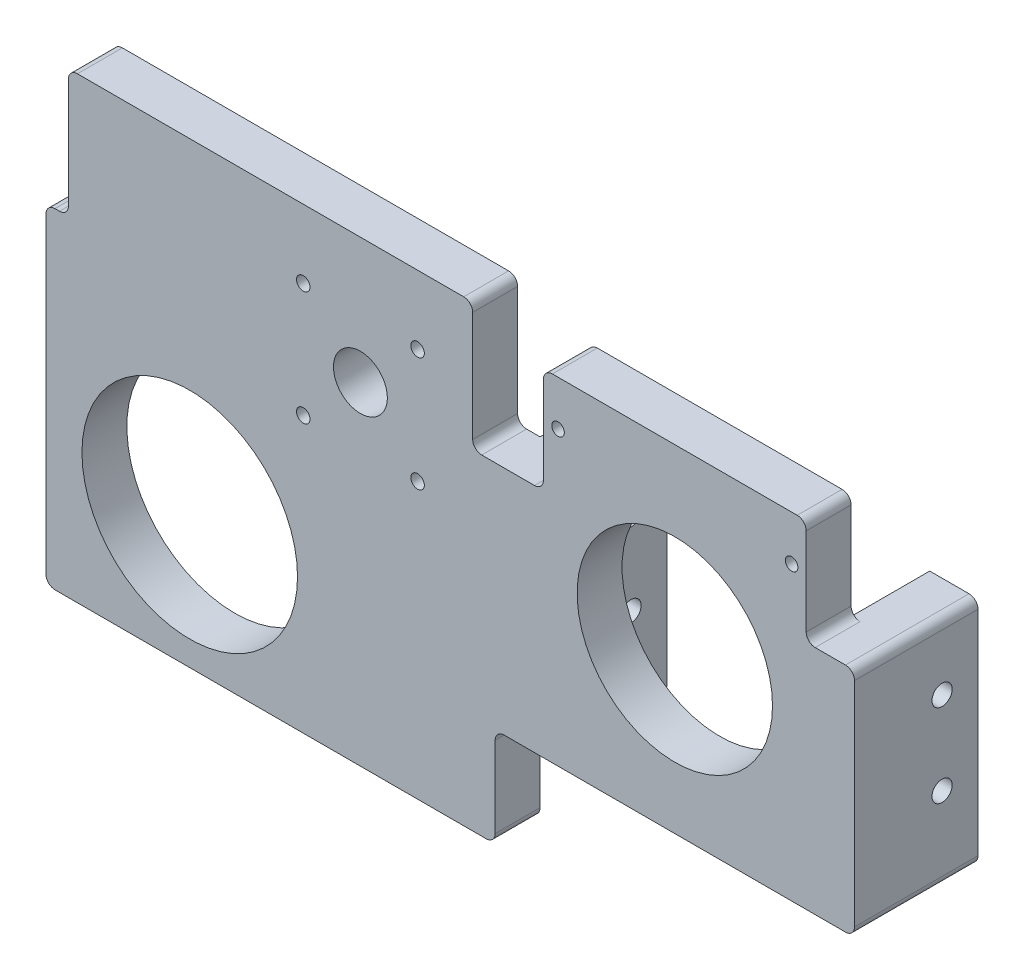
SolidWorks part; units mm, degrees
ref_plane "Front Plane" through (0, 0, 0) normal (0, 0, 1) x (1, 0, 0)
ref_plane "Top Plane" through (0, 0, 0) normal (0, 1, 0) x (1, 0, 0)
ref_plane "Right Plane" through (0, 0, 0) normal (1, 0, 0) x (0, 0, -1)
sketch "Sketch1" plane through (0, 0, 0) normal (0, 1, 0) x (1, 0, 0)
  line L0 (0, 0) -> (0, -3.75) construction
  line L1 (-40, -13.75) -> (40, -13.75)
  line L2 (-40, -13.75) -> (-40, 13.75)
  line L3 (-40, 13.75) -> (-29.25, 13.75)
  line L4 (40, -13.75) -> (40, 13.75)
  line L5 (-40, -13.75) -> (40, 13.75) construction
  line L6 (-40, 13.75) -> (40, -13.75) construction
  line L8 (-29.25, 13.75) -> (-29.25, -3.75)
  line L9 (-29.25, -3.75) -> (29.25, -3.75)
  line L10 (29.25, 13.75) -> (29.25, -3.75)
  line L11 (29.25, 13.75) -> (40, 13.75)
  point P0 (0, 0)
  dimension "D1" = 80
  dimension "D2" = 27.5
  dimension "D3" = 10.75
  dimension "D4" = 10
extrude "Boss-Extrude1" add sketch "Sketch1" along normal blind 80
sketch "Sketch2" plane through (0, 0, 13.75) normal (0, 0, 1) x (1, 0, 0)
  line L0 (0, 0) -> (0, 35.5) construction
  line L1 (-40, 0) -> (40, 0) construction
  circle A0 centre (0, 35.5) radius 21.75
  dimension "D2" = 43.5
  dimension "D1" = 35.5
extrude "Cut-Extrude1" cut sketch "Sketch2" against normal blind 10
sketch "Sketch3" plane through (0, 0, 13.75) normal (0, 0, 1) x (1, 0, 0)
  line L0 (0, 35.5) -> (0, 80) construction
  line L1 (-40, 80) -> (40, 80) construction
  line L2 (0, 65) -> (26, 65) construction
  circle A1 centre (26, 65) radius 1.4
  circle A2 centre (-26, 65) radius 1.4
  dimension "D1" = 26
  dimension "D3" = 2.8
  dimension "D2" = 29.5
extrude "Cut-Extrude2" cut sketch "Sketch3" against normal blind 4
sketch "Sketch4" plane through (0, 0, 3.75) normal (0, 0, -1) x (-1, 0, 0)
  line L0 (0, 35.5) -> (0, 80) construction
  line L1 (-29.25, 80) -> (29.25, 80) construction
  line L2 (-29.25, 65) -> (29.25, 65) construction
  line L3 (29.25, 80) -> (29.25, 0) construction
  line L4 (-27.21, 62.9042) -> (-28.42, 65)
  line L5 (28.42, 65) -> (27.21, 67.0958)
  line L6 (27.21, 67.0958) -> (24.79, 67.0958)
  line L7 (24.79, 67.0958) -> (23.58, 65)
  line L8 (23.58, 65) -> (24.79, 62.9042)
  line L9 (24.79, 62.9042) -> (27.21, 62.9042)
  line L10 (27.21, 62.9042) -> (28.42, 65)
  line L11 (-24.79, 62.9042) -> (-27.21, 62.9042)
  line L12 (-23.58, 65) -> (-24.79, 62.9042)
  line L13 (-24.79, 67.0958) -> (-23.58, 65)
  line L14 (-27.21, 67.0958) -> (-24.79, 67.0958)
  line L15 (-28.42, 65) -> (-27.21, 67.0958)
  circle A0 centre (26, 65) radius 2.0958 construction
  circle A1 centre (-26, 65) radius 2.0958 construction
  point P21 (0, 65)
  dimension "D1" = 29.5
  dimension "D2" = 26
  dimension "D3" = 2.42
extrude "Cut-Extrude3" cut sketch "Sketch4" against normal blind 6
sketch "Sketch5" plane through (40, 0, 0) normal (1, 0, 0) x (0, 0, -1)
  line L0 (5.75, 0) -> (5.75, 80) construction
  line L1 (-13.75, 0) -> (13.75, 0) construction
  line L2 (-13.75, 80) -> (13.75, 80) construction
  line L3 (-13.75, 80) -> (-13.75, 0) construction
  circle A0 centre (5.75, 18.5) radius 2.25
  circle A1 centre (5.75, 37) radius 2.25
  dimension "D3" = 4.5
  dimension "D1" = 18.5
  dimension "D2" = 18.5
  dimension "D4" = 19.5
extrude "Cut-Extrude4" cut sketch "Sketch5" against normal through all
sketch "Sketch6" plane through (0, 0, 13.75) normal (0, 0, 1) x (1, 0, 0)
  line L0 (0, 0) -> (0, 80) construction
  line L1 (-40, 80) -> (-29.25, 80)
  line L2 (-40, 80) -> (-40, 51.5)
  line L3 (-40, 51.5) -> (-29.25, 51.5)
  line L4 (-29.25, 80) -> (-29.25, 51.5)
  line L5 (-40, 0) -> (40, 0) construction
  line L6 (-40, 80) -> (40, 80) construction
  line L7 (40, 51.5) -> (29.25, 51.5)
  line L8 (40, 80) -> (29.25, 80)
  line L9 (29.25, 80) -> (29.25, 51.5)
  line L10 (40, 80) -> (40, 51.5)
  dimension "D1" = 10.75
  dimension "D2" = 28.5
extrude "Cut-Extrude5" cut sketch "Sketch6" against normal through all
sketch "Sketch7" plane through (-40, 0, 0) normal (-1, 0, 0) x (0, 0, 1)
  line L0 (3.75, 0) -> (3.75, -22)
  line L2 (13.75, 0) -> (13.75, 80)
  line L3 (13.75, 80) -> (3.75, 80)
  line L4 (3.75, 0) -> (3.75, 80)
  line L5 (3.75, -22) -> (13.75, -22)
  line L6 (13.75, -22) -> (13.75, 0)
  line L7 (-13.75, 0) -> (13.75, 0) construction
  dimension "D1" = 22
extrude "Boss-Extrude2" add sketch "Sketch7" along normal blind 100
sketch "Sketch8" plane through (0, 0, 13.75) normal (0, 0, 1) x (1, 0, 0)
  line L0 (-140, -22) -> (-140, 80) construction
  line L2 (-45, 80) -> (-45, 51.5)
  line L3 (-140, 80) -> (-40, 80) construction
  line L4 (-45, 51.5) -> (-40, 51.5)
  line L6 (-45, 80) -> (-40, 80)
  line L7 (-40, 80) -> (-40, 51.5)
  line L8 (-135, 51.5) -> (-140, 51.5)
  line L9 (-140, 80) -> (-140, 51.5)
  line L10 (-135, 80) -> (-140, 80)
  line L11 (-135, 80) -> (-135, 51.5)
  dimension "D1" = 5
extrude "Cut-Extrude6" cut sketch "Sketch8" against normal blind 80
sketch "Sketch9" plane through (0, 0, 13.75) normal (0, 0, 1) x (1, 0, 0)
  line L3 (0, 35.5) -> (-108, 35.5) construction
  line L4 (-108, 35.5) -> (-108, 7.5) construction
  circle A0 centre (-108, 7.5) radius 24
  dimension "D1" = 48
  dimension "D2" = 108
  dimension "D3" = 28
extrude "Cut-Extrude7" cut sketch "Sketch9" against normal blind 80
sketch "Sketch10" plane through (0, 0, 13.75) normal (0, 0, 1) x (1, 0, 0)
  line L0 (-108, 7.5) -> (-108, 37.5) construction
  line L1 (-108, 37.5) -> (-88, 37.5) construction
  circle A0 centre (-88, 37.5) radius 11
  dimension "D3" = 22
  dimension "D1" = 30
  dimension "D2" = 20
extrude "Cut-Extrude8" [suppressed] cut sketch "Sketch10" against normal blind 5
sketch "Sketch12" plane through (0, 0, 13.75) normal (0, 0, 1) x (1, 0, 0)
  line L0 (-108, 7.5) -> (-108, 52) construction
  line L1 (-108, 52) -> (-70, 52) construction
  line L2 (-70, 52) -> (-85.9099, 67.9099) construction
  line L3 (-70, 52) -> (-92.6274, 74.6274) construction
  circle A0 centre (-70, 52) radius 6
  dimension "D3" = 12
  dimension "D1" = 44.5
  dimension "D2" = 38
  dimension "D4" = 22.5
  dimension "D5" = 45
  dimension "D6" = 32
extrude "Cut-Extrude9" cut sketch "Sketch12" against normal blind 28
sketch "Sketch13" plane through (0, 0, 13.75) normal (0, 0, 1) x (1, 0, 0)
  line L0 (29.25, 80) -> (29.25, 51.5) construction
  line L1 (-29.25, 80) -> (29.25, 80)
  line L2 (-29.25, 80) -> (-29.25, 75)
  line L3 (-29.25, 75) -> (29.25, 75)
  line L4 (29.25, 80) -> (29.25, 75)
  dimension "D1" = 5
extrude "Cut-Extrude10" cut sketch "Sketch13" against normal through all
fillet "Fillet2" radius 2 14 edges at (-40, 0, 8.75) (-135, 51.5, 8.75) (29.25, 51.5, 8.75) (-29.25, 51.5, 8.75) (-45, 51.5, 8.75) (-135, 80, 8.75) (-45, 80, 8.75) (-29.25, 75, 8.75) (29.25, 75, 8.75) (-140, -22, 8.75) (-40, -22, 8.75) (-140, 51.5, 8.75) (40, 51.5, 0) (40, 0, 0)
sketch "Sketch15" plane through (0, 0, 13.75) normal (0, 0, 1) x (1, 0, 0)
  line L0 (-70, 52) -> (-70, 66.25) construction
  line L1 (-70, 52) -> (-50.75, 52) construction
  line L2 (-70, 52) -> (-57.2721, 64.7279) construction
  circle A1 centre (-57.2721, 64.7279) radius 1.5
  circle A2 centre (-57.2721, 39.2721) radius 1.5
  circle A3 centre (-82.7279, 39.2721) radius 1.5
  circle A4 centre (-82.7279, 64.7279) radius 1.5
  point P16 (-70, 52)
  dimension "D3" = 3
  dimension "D2" = 45
  dimension "D4" = 18
  dimension "D5" = 4
extrude "Cut-Extrude11" cut sketch "Sketch15" against normal through all
